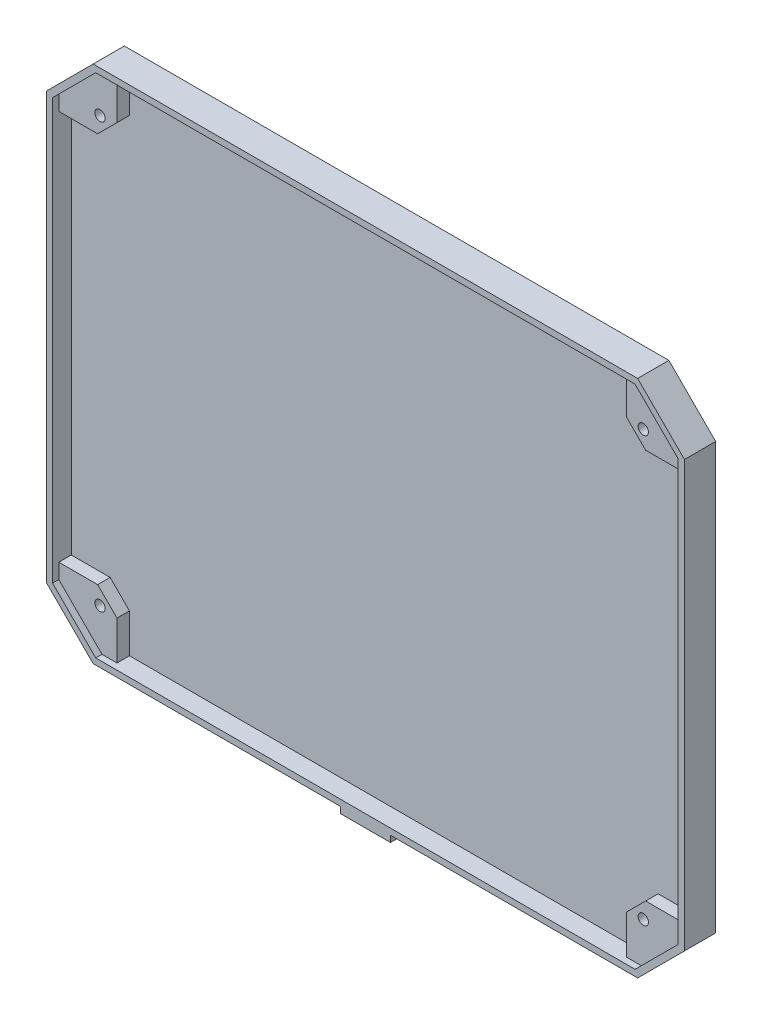
SolidWorks part; units mm, degrees
ref_plane "Plan de face" through (0, 0, 0) normal (0, 0, 1) x (1, 0, 0)
ref_plane "Plan de dessus" through (0, 0, 0) normal (0, 1, 0) x (1, 0, 0)
ref_plane "Plan de droite" through (0, 0, 0) normal (1, 0, 0) x (0, 0, -1)
sketch "Esquisse1" plane through (0, 0, 0) normal (0, 0, 1) x (1, 0, 0)
  line L0 (-102.26, 83.21) -> (102.26, -83.21) construction
  line L1 (-102.26, 83.21) -> (102.26, 83.21)
  line L2 (-102.26, 83.21) -> (-102.26, -83.21)
  line L3 (-102.26, -83.21) -> (102.26, -83.21)
  line L4 (102.26, 83.21) -> (102.26, -83.21)
  dimension "D1" = 166.42
  dimension "D2" = 204.52
extrude "Boss.-Extru.1" add sketch "Esquisse1" along normal blind 10
chamfer "Chanfrein1" distance 15 angle 45 4 edges at (102.26, 83.21, 5) (102.26, -83.21, 5) (-102.26, -83.21, 5) (-102.26, 83.21, 5)
sketch "Esquisse2" plane through (0, 0, 10) normal (0, 0, 1) x (1, 0, 0)
  line L0 (86.4316, -81.21) -> (100.26, -67.3816)
  line L1 (100.26, -67.3816) -> (100.26, 67.3816)
  line L2 (100.26, 67.3816) -> (86.4316, 81.21)
  line L3 (86.4316, 81.21) -> (-86.4316, 81.21)
  line L4 (-86.4316, 81.21) -> (-100.26, 67.3816)
  line L5 (-100.26, 67.3816) -> (-100.26, -67.3816)
  line L6 (-100.26, -67.3816) -> (-86.4316, -81.21)
  line L7 (-86.4316, -81.21) -> (86.4316, -81.21)
  line L8 (102.26, -68.21) -> (102.26, 68.21) construction
  line L9 (-87.26, -83.21) -> (87.26, -83.21) construction
  line L10 (102.26, 68.21) -> (87.26, 83.21) construction
  line L11 (87.26, 83.21) -> (-87.26, 83.21) construction
  line L12 (-87.26, 83.21) -> (-102.26, 68.21) construction
  line L13 (-102.26, 68.21) -> (-102.26, -68.21) construction
  line L14 (87.26, -83.21) -> (102.26, -68.21) construction
  line L15 (-102.26, -68.21) -> (-87.26, -83.21) construction
  dimension "D1" = 2
  dimension "D2" = 2
  dimension "D3" = 2
  dimension "D4" = 2
  dimension "D5" = 2
  dimension "D6" = 2
  dimension "D7" = 2
  dimension "D8" = 2
extrude "Enlèv. mat.-Extru.1" cut sketch "Esquisse2" against normal blind 2
sketch "Esquisse3" plane through (0, 0, 8) normal (0, 0, 1) x (1, 0, 0)
  line L0 (-81.6116, 81.21) -> (-81.6116, 68.7625)
  line L1 (86.4316, 81.21) -> (-86.4316, 81.21) construction
  line L2 (-81.6116, 68.7625) -> (-87.8125, 62.5616)
  line L3 (-87.8125, 62.5616) -> (-100.26, 62.5616)
  line L4 (-100.26, 67.3816) -> (-100.26, -67.3816) construction
  line L6 (-86.4316, 81.21) -> (-100.26, 67.3816) construction
  line L7 (-86.4316, 81.21) -> (-100.26, 67.3816) construction
  line L8 (0, 0) -> (0, 81.21) construction
  line L9 (86.4316, 81.21) -> (-86.4316, 81.21) construction
  line L10 (0, 0) -> (-100.26, 0) construction
  line L11 (-100.26, 67.3816) -> (-100.26, -67.3816) construction
  line L12 (87.8125, 62.5616) -> (100.26, 62.5616)
  line L13 (81.6116, 68.7625) -> (87.8125, 62.5616)
  line L14 (81.6116, 81.21) -> (81.6116, 68.7625)
  line L15 (87.8125, -62.5616) -> (100.26, -62.5616)
  line L16 (81.6116, -68.7625) -> (87.8125, -62.5616)
  line L17 (81.6116, -81.21) -> (81.6116, -68.7625)
  line L18 (-87.8125, -62.5616) -> (-100.26, -62.5616)
  line L19 (-81.6116, -68.7625) -> (-87.8125, -62.5616)
  line L20 (-81.6116, -81.21) -> (-81.6116, -68.7625)
  line L21 (-100.26, 62.5616) -> (-100.26, -62.5616)
  line L22 (100.26, 62.5616) -> (100.26, -62.5616)
  line L23 (81.6116, -81.21) -> (-81.6116, -81.21)
  line L24 (-81.6116, 81.21) -> (81.6116, 81.21)
  dimension "D1" = 4.82
  dimension "D2" = 4.82
  dimension "D3" = 12.21
extrude "Enlèv. mat.-Extru.2" cut sketch "Esquisse3" against normal blind 4
sketch "Esquisse4" plane through (0, 0, 8) normal (0, 0, 1) x (1, 0, 0)
  line L0 (0, 0) -> (-99.3595, 0) construction
  line L1 (0, 0) -> (0, 55.116) construction
  circle A0 centre (-87.06, 68.01) radius 1.65
  circle A1 centre (-87.06, -68.01) radius 1.65
  circle A2 centre (87.06, -68.01) radius 1.65
  circle A3 centre (87.06, 68.01) radius 1.65
  point P12 (0, 0)
  point P13 (0, 0)
  dimension "D1" = 136.02
  dimension "D2" = 174.12
  dimension "D3" = 3.3
extrude "Enlèv. mat.-Extru.3" cut sketch "Esquisse4" against normal through all
sketch "Esquisse5" plane through (0, 0, 0) normal (0, 0, -1) x (-1, 0, 0)
  circle A0 centre (87.06, 68.01) radius 3.8
  circle A1 centre (-87.06, 68.01) radius 3.8
  circle A2 centre (-87.06, -68.01) radius 3.8
  circle A3 centre (87.06, -68.01) radius 3.8
  dimension "D1" = 7.6
extrude "Enlèv. mat.-Extru.4" cut sketch "Esquisse5" against normal blind 2.8
sketch "Esquisse6" plane through (0, -83.21, 0) normal (0, -1, 0) x (1, 0, 0)
  line L0 (-87.26, 10) -> (87.26, 10) construction
  line L1 (-8.05, 10) -> (8.05, 10)
  line L2 (-8.05, 10) -> (-8.05, 7)
  line L3 (-8.05, 7) -> (8.05, 7)
  line L4 (8.05, 10) -> (8.05, 7)
  line L5 (0, 10) -> (0, 7) construction
  dimension "D1" = 3
  dimension "D2" = 16.1
extrude "Boss.-Extru.2" add sketch "Esquisse6" along normal blind 2
